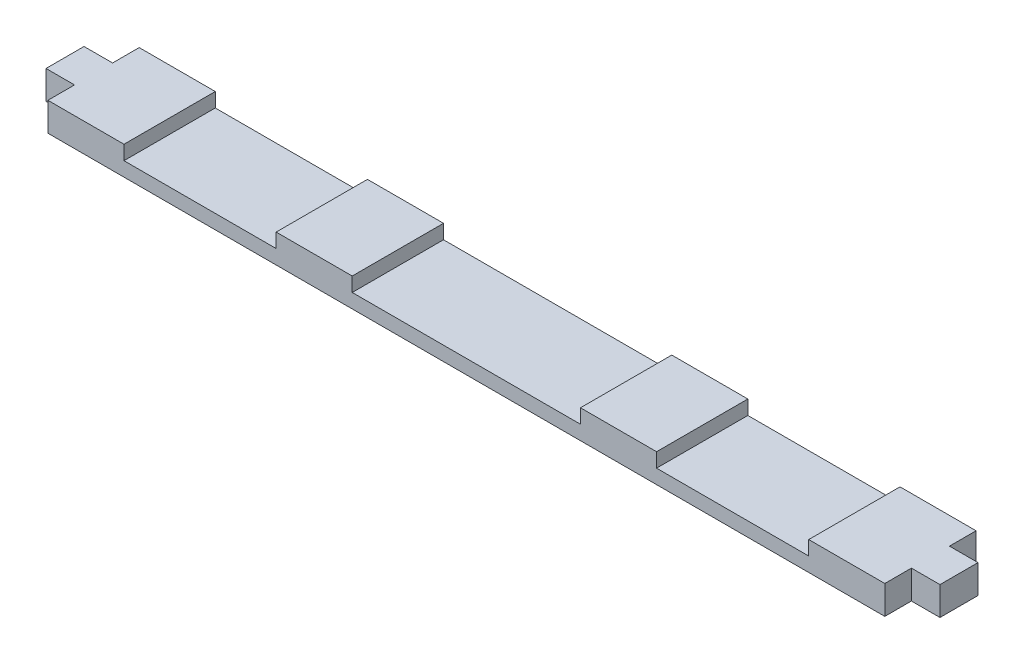
SolidWorks part; units mm, degrees
ref_plane "Front Plane" through (0, 0, 0) normal (0, 0, 1) x (1, 0, 0)
ref_plane "Top Plane" through (0, 0, 0) normal (0, 1, 0) x (1, 0, 0)
ref_plane "Right Plane" through (0, 0, 0) normal (1, 0, 0) x (0, 0, -1)
sketch "Sketch1" plane through (0, 0, 0) normal (0, 1, 0) x (1, 0, 0)
  line L1 (139.7, -15.24) -> (-139.7, -15.24)
  line L2 (139.7, -15.24) -> (139.7, 15.24)
  line L3 (139.7, 15.24) -> (-139.7, 15.24)
  line L4 (-139.7, -15.24) -> (-139.7, 15.24)
  line L5 (139.7, -15.24) -> (-139.7, 15.24) construction
  line L6 (139.7, 15.24) -> (-139.7, -15.24) construction
  point P0 (0, 0)
  dimension "D1" = 279.4
  dimension "D2" = 30.48
extrude "Boss-Extrude1" add sketch "Sketch1" along normal blind 9.525
sketch "Sketch2" plane through (139.7, 0, 0) normal (1, 0, 0) x (0, 0, -1)
  line L0 (-15.24, 0) -> (15.24, 0) construction
  line L1 (-6.35, 0) -> (6.35, 0)
  line L2 (-6.35, 0) -> (-6.35, 9.525)
  line L3 (-6.35, 9.525) -> (6.35, 9.525)
  line L4 (6.35, 0) -> (6.35, 9.525)
  line L5 (-15.24, 9.525) -> (15.24, 9.525) construction
  line L6 (-15.24, 9.525) -> (-15.24, 0) construction
  dimension "D1" = 12.7
  dimension "D2" = 8.89
extrude "Boss-Extrude2" add sketch "Sketch2" along normal blind 9.525
mirror "Mirror1" about plane through (0, 0, 0) normal (1, 0, 0) of "Boss-Extrude2"
sketch "Sketch3" plane through (0, 0, 0) normal (0, -1, 0) x (1, 0, 0)
  line L0 (-138.2612, -11.4174) -> (137.3788, -11.4174)
sketch "Sketch4" plane through (0, 9.525, 0) normal (0, 1, 0) x (1, 0, 0)
  line L0 (139.7, 15.24) -> (-139.7, 15.24) construction
  line L1 (-38.1, 15.24) -> (38.1, 15.24)
  line L2 (-38.1, 15.24) -> (-38.1, -15.24)
  line L3 (-38.1, -15.24) -> (38.1, -15.24)
  line L4 (38.1, 15.24) -> (38.1, -15.24)
  line L5 (-139.7, -15.24) -> (139.7, -15.24) construction
  line L6 (-139.7, 15.24) -> (-139.7, 6.35) construction
  line L7 (63.5, 15.24) -> (114.3, 15.24)
  line L8 (63.5, 15.24) -> (63.5, -15.24)
  line L9 (63.5, -15.24) -> (114.3, -15.24)
  line L10 (114.3, 15.24) -> (114.3, -15.24)
  line L11 (-114.3, 15.24) -> (-63.5, 15.24)
  line L12 (-114.3, 15.24) -> (-114.3, -15.24)
  line L13 (-114.3, -15.24) -> (-63.5, -15.24)
  line L14 (-63.5, 15.24) -> (-63.5, -15.24)
  line L15 (139.7, -15.24) -> (139.7, -6.35) construction
  point P18 (-38.1, 0)
  dimension "D1" = 25.4
  dimension "D2" = 25.4
  dimension "D3" = 25.4
  dimension "D4" = 25.4
  dimension "D5" = 38.1
  dimension "D6" = 38.1
extrude "Cut-Extrude1" cut sketch "Sketch4" against normal blind 4.7625
